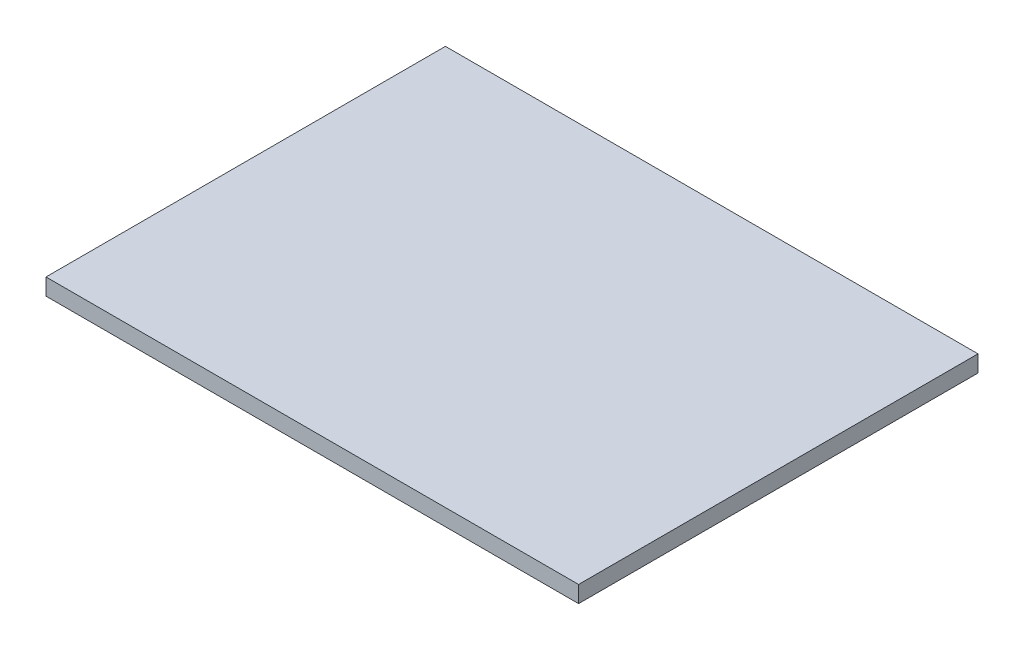
SolidWorks part; units mm, degrees
ref_plane "Спереди" through (0, 0, 0) normal (0, 0, 1) x (1, 0, 0)
ref_plane "Сверху" through (0, 0, 0) normal (0, 1, 0) x (1, 0, 0)
ref_plane "Справа" through (0, 0, 0) normal (1, 0, 0) x (0, 0, -1)
sketch "Эскиз1" plane through (0, 0, 0) normal (0, 1, 0) x (1, 0, 0)
  line L1 (-40, 30) -> (40, 30)
  line L2 (-40, 30) -> (-40, -30)
  line L3 (-40, -30) -> (40, -30)
  line L4 (40, 30) -> (40, -30)
  line L5 (-40, 30) -> (40, -30) construction
  line L6 (-40, -30) -> (40, 30) construction
  point P0 (0, 0)
extrude "Бобышка-Вытянуть1" add sketch "Эскиз1" along normal blind 2.5
